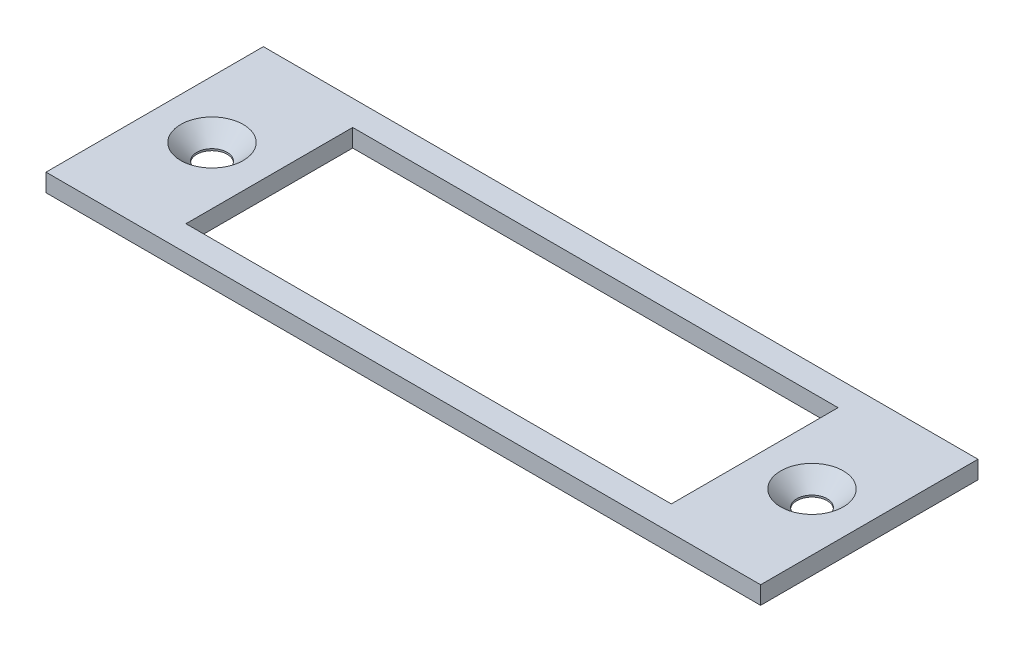
SolidWorks part; units mm, degrees
ref_plane "Front Plane" through (0, 0, 0) normal (0, 0, 1) x (1, 0, 0)
ref_plane "Top Plane" through (0, 0, 0) normal (0, 1, 0) x (1, 0, 0)
ref_plane "Right Plane" through (0, 0, 0) normal (1, 0, 0) x (0, 0, -1)
sketch "Sketch1" plane through (0, 0, 0) normal (0, 1, 0) x (1, 0, 0)
  line L1 (0, 0) -> (120, 0)
  line L2 (0, 0) -> (0, -36.5)
  line L3 (0, -36.5) -> (120, -36.5)
  line L4 (120, 0) -> (120, -36.5)
  dimension "D1" = 120
  dimension "D2" = 36.5
extrude "Boss-Extrude1" add sketch "Sketch1" along normal blind 3
sketch "Sketch2" plane through (0, 3, 0) normal (0, 1, 0) x (1, 0, 0)
  line L0 (0, -18.25) -> (120, -18.25) construction
  line L1 (0, 0) -> (0, -36.5) construction
  line L2 (120, -36.5) -> (120, 0) construction
  line L3 (19.25, -32.25) -> (100.75, -32.25)
  line L4 (60, -18.25) -> (60, -4.25) construction
  line L5 (60, -4.25) -> (100.75, -4.25)
  line L6 (60, -4.25) -> (19.25, -4.25)
  line L7 (19.25, -4.25) -> (19.25, -32.25)
  line L8 (100.75, -32.25) -> (100.75, -4.25)
extrude "Cut-Extrude1" cut sketch "Sketch2" against normal through all
sketch "Sketch4" plane through (0, 3, 0) normal (0, 1, 0) x (1, 0, 0)
  line L0 (0, -18.25) -> (19.25, -18.25)
  line L1 (0, 0) -> (0, -36.5) construction
  line L2 (19.25, -4.25) -> (19.25, -32.25) construction
  line L3 (19.25, -18.25) -> (9.625, -18.25)
  line L4 (9.625, -18.25) -> (9.625, 0)
  line L5 (120, 0) -> (0, 0) construction
  line L6 (100.75, -18.25) -> (120, -18.25)
  line L7 (100.75, -32.25) -> (100.75, -4.25) construction
  line L8 (120, -36.5) -> (120, 0) construction
  line L9 (120, -18.25) -> (110.375, -18.25)
  line L10 (110.375, -18.25) -> (110.375, 0)
hole_wizard "CSK for #5 Oval Head Machine Screw1" positions "Sketch5" profile "Sketch6" countersink size "#5" standard "ANSI Inch" end condition through all
sketch "Sketch5" plane through (0, 3, 0) normal (0, 1, 0) x (1, 0, 0)
  point P0 (9.625, -18.25)
  point P3 (110.375, -18.25)
sketch "Sketch6" plane through (9.625, 3, 18.25) normal (1, 0, 0) x (0, 0, 1)
  line L0 (0, 0) -> (0, 3)
  line L1 (0, 3) -> (2.55, 3)
  line L2 (2.55, 3) -> (2.55, 2.7)
  line L3 (2.55, 2.7) -> (5.25, 0)
  line L5 (5.25, 0) -> (0, 0)
  line L6 (-2.55, 2.7) -> (-5.25, 0) construction
  line L11 (0, -6.35) -> (0, 107.95) construction
  dimension "Thru Hole Dia." = 5.1
  dimension "Thru Hole Depth" = 3
  dimension "Near C'Sink Dia." = 10.5
  dimension "Near C'Sink Angle" = 90
